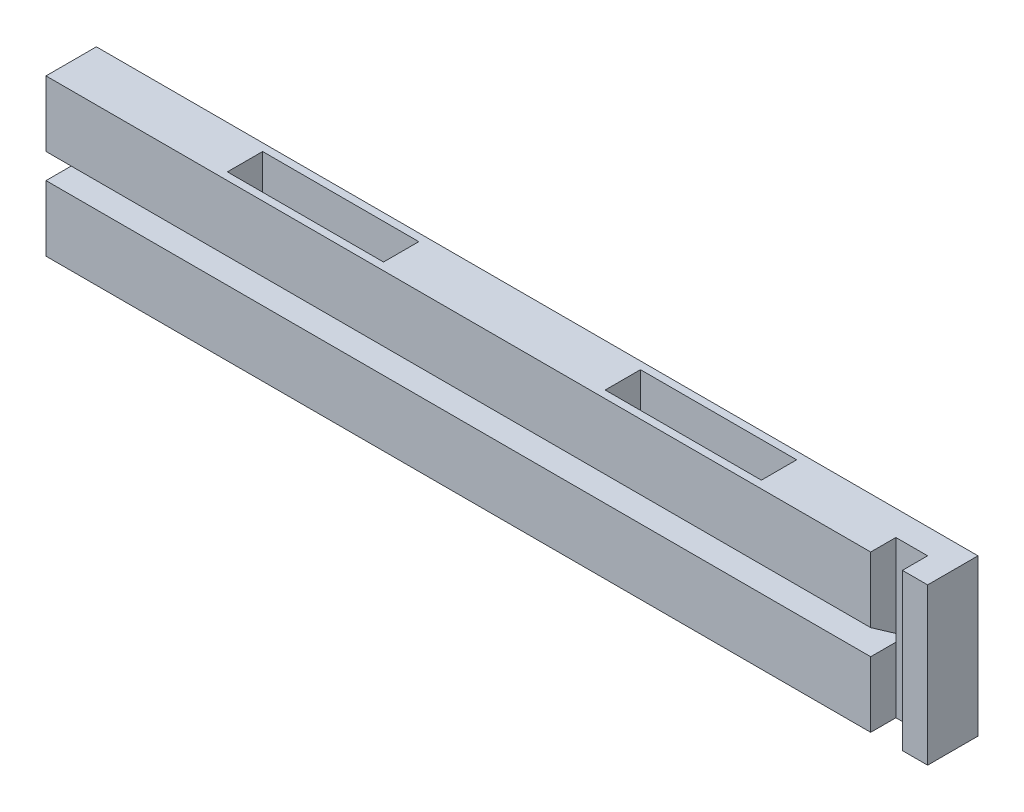
SolidWorks part; units mm, degrees
material "ABS"
ref_plane "Plano frontal" through (0, 0, 0) normal (0, 0, 1) x (1, 0, 0)
ref_plane "Plano superior" through (0, 0, 0) normal (0, 1, 0) x (1, 0, 0)
ref_plane "Plano direito" through (0, 0, 0) normal (1, 0, 0) x (0, 0, -1)
sketch "Esboço1" plane through (0, 0, 0) normal (0, 0, 1) x (1, 0, 0)
  line L1 (87.5, -15.5) -> (-87.5, -15.5)
  line L2 (87.5, -15.5) -> (87.5, 15.5)
  line L3 (87.5, 15.5) -> (-87.5, 15.5)
  line L4 (-87.5, -15.5) -> (-87.5, 15.5)
  line L5 (87.5, -15.5) -> (-87.5, 15.5) construction
  line L6 (87.5, 15.5) -> (-87.5, -15.5) construction
  point P0 (0, 0)
  dimension "D1" = 175
  dimension "D2" = 31
extrude "Ressalto-extrusão1" add sketch "Esboço1" along normal blind 10
sketch "Esboço2" plane through (0, 15.5, 0) normal (0, 1, 0) x (1, 0, 0)
  line L0 (-111.1236, -5) -> (103.3487, -5) construction
  line L1 (0, 16.6179) -> (0, -31.1724) construction
  line L2 (87.5, 0) -> (-87.5, 0) construction
  line L3 (-87.5, -10) -> (-87.5, 0) construction
  line L4 (-22, -8.5) -> (-53, -8.5)
  line L5 (-22, -8.5) -> (-22, -1.5)
  line L6 (-22, -1.5) -> (-53, -1.5)
  line L7 (-53, -8.5) -> (-53, -1.5)
  line L8 (-22, -8.5) -> (-53, -1.5) construction
  line L9 (-22, -1.5) -> (-53, -8.5) construction
  line L10 (22, -1.5) -> (53, -8.5) construction
  line L11 (22, -8.5) -> (53, -1.5) construction
  line L12 (53, -8.5) -> (53, -1.5)
  line L13 (22, -1.5) -> (53, -1.5)
  line L14 (22, -8.5) -> (22, -1.5)
  line L15 (22, -8.5) -> (53, -8.5)
  point P7 (-37.5, -5)
  point P21 (37.5, -5)
  dimension "D1" = 5
  dimension "D2" = 7
  dimension "D3" = 31
  dimension "D4" = 50
extrude "Corte-extrusão1" cut sketch "Esboço2" against normal blind 10.5
sketch "Esboço3" plane through (0, -15.5, 0) normal (0, -1, 0) x (1, 0, 0)
  line L0 (-105.0554, 5) -> (100.316, 5) construction
  line L1 (-87.5, 10) -> (87.5, 10) construction
  line L2 (0, 21.6875) -> (0, -29.1463) construction
  line L3 (-87.5, 10) -> (-87.5, 0) construction
  line L4 (-22, 1.5) -> (-53, 1.5)
  line L5 (-22, 1.5) -> (-22, 8.5)
  line L6 (-22, 8.5) -> (-53, 8.5)
  line L7 (-53, 1.5) -> (-53, 8.5)
  line L8 (-22, 1.5) -> (-53, 8.5) construction
  line L9 (-22, 8.5) -> (-53, 1.5) construction
  line L10 (22, 8.5) -> (53, 1.5) construction
  line L11 (22, 1.5) -> (53, 8.5) construction
  line L12 (53, 1.5) -> (53, 8.5)
  line L13 (22, 8.5) -> (53, 8.5)
  line L14 (22, 1.5) -> (22, 8.5)
  line L15 (22, 1.5) -> (53, 1.5)
  point P6 (-37.5, 5)
  point P19 (37.5, 5)
  dimension "D1" = 5
  dimension "D2" = 7
  dimension "D3" = 31
  dimension "D4" = 50
extrude "Corte-extrusão2" cut sketch "Esboço3" against normal blind 10.5
sketch "Esboço5" plane through (-87.5, 0, 0) normal (-1, 0, 0) x (0, 0, 1)
  line L0 (5, 26.6629) -> (5, -26.0741) construction
  line L1 (10, 15.5) -> (10, -15.5) construction
  line L2 (10, 15.5) -> (0, 15.5) construction
  line L3 (27.0388, 0) -> (-12.2765, 0) construction
  circle A0 centre (5, 10.5) radius 1.5
  circle A1 centre (5, -10.5) radius 1.5
  dimension "D2" = 3
  dimension "D1" = 5
  dimension "D3" = 5
extrude "Corte-extrusão4" cut sketch "Esboço5" against normal blind 8
sketch "Esboço7" plane through (0, 0, 10) normal (0, 0, 1) x (1, 0, 0)
  line L0 (-108.2791, 0) -> (108.474, 0) construction
  line L1 (0, 34.892) -> (0, -42.8649) construction
  line L2 (87.5, 15.5) -> (-87.5, 15.5) construction
  line L3 (82.5, -15.5) -> (76.2, -15.5)
  line L4 (82.5, -15.5) -> (82.5, 15.5)
  line L5 (82.5, 15.5) -> (76.2, 15.5)
  line L6 (76.2, -15.5) -> (76.2, 15.5)
  line L7 (82.5, -15.5) -> (76.2, 15.5) construction
  line L8 (82.5, 15.5) -> (76.2, -15.5) construction
  line L9 (87.5, -15.5) -> (87.5, 15.5) construction
  point P4 (79.35, 0)
  dimension "D1" = 6.3
  dimension "D2" = 5
extrude "Corte-extrusão6" cut sketch "Esboço7" against normal blind 5
sketch "Esboço8" plane through (-87.5, 0, 0) normal (-1, 0, 0) x (0, 0, 1)
  line L0 (-5.5136, 0) -> (19.9874, 0) construction
  line L1 (10, 2.5) -> (2.8593, -2.5)
  line L3 (5, 27.7359) -> (5, -27.8467) construction
  line L4 (0, 15.5) -> (0, -15.5) construction
  line L7 (2.8593, -2.5) -> (10, -2.5)
  line L8 (10, 15.5) -> (10, -15.5) construction
  line L9 (10, 2.5) -> (10, -2.5)
  point P15 (6.4296, 0)
  dimension "D1" = 5
  dimension "D2" = 55
  dimension "D3" = 5
extrude "Corte-extrusão7" cut sketch "Esboço8" against normal up to surface (163.7 mm away) up to face at (76.2, 0, 7.5)
